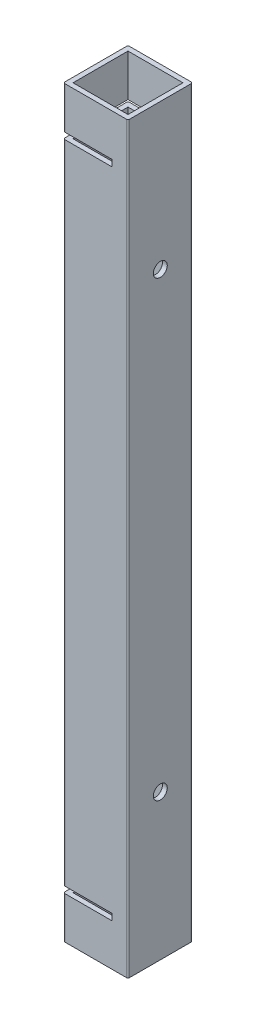
SolidWorks part; units mm, degrees
ref_plane "Front Plane" through (0, 0, 0) normal (0, 0, 1) x (1, 0, 0)
ref_plane "Top Plane" through (0, 0, 0) normal (0, 1, 0) x (1, 0, 0)
ref_plane "Right Plane" through (0, 0, 0) normal (1, 0, 0) x (0, 0, -1)
sketch "Sketch1" plane through (0, 0, 0) normal (0, 1, 0) x (1, 0, 0)
  line L0 (1.5, 1.5) -> (18.5, 1.5)
  line L1 (0.5, 0) -> (19.5, 0)
  line L2 (0, 0.5) -> (0, 19.5)
  line L3 (0.5, 20) -> (19.5, 20)
  line L4 (20, 0.5) -> (20, 19.5)
  line L5 (18.5, 1.5) -> (18.5, 18.5)
  line L6 (1.5, 18.5) -> (18.5, 18.5)
  line L7 (1.5, 1.5) -> (1.5, 18.5)
  arc A0 (19.5, 0) -> (20, 0.5) centre (19.5, 0.5) ccw
  arc A1 (0.5, 0) -> (0, 0.5) centre (0.5, 0.5) cw
  arc A2 (0, 19.5) -> (0.5, 20) centre (0.5, 19.5) cw
  arc A3 (19.5, 20) -> (20, 19.5) centre (19.5, 19.5) cw
  arc A4 (18.5, 1.5) -> (18.5, 1.5) centre (18.5, 1.5) ccw
  arc A5 (18.5, 18.5) -> (18.5, 18.5) centre (18.5, 18.5) cw
  arc A6 (1.5, 18.5) -> (1.5, 18.5) centre (1.5, 18.5) cw
  arc A7 (1.5, 1.5) -> (1.5, 1.5) centre (1.5, 1.5) cw
  point P9 (0, 0)
  dimension "D3" = 0.5
  dimension "D1" = 20
  dimension "D2" = 20
  dimension "D4" = 1.5
extrude "Boss-Extrude1" add sketch "Sketch1" along normal blind 230
sketch "Sketch2" plane through (0, 0, 0) normal (-1, 0, 0) x (0, 0, 1)
  line L0 (-0.5, 115) -> (-19.5, 115) construction
  line L5 (-0.5, 230) -> (-0.5, 0) construction
  line L6 (-19.5, 230) -> (-19.5, 0) construction
  line L12 (0, 15) -> (-20, 15)
  line L18 (0, 230) -> (0, 0) construction
  line L19 (-20, 230) -> (-20, 0) construction
  line L20 (-20, 15) -> (-20, 13)
  line L21 (-20, 13) -> (0, 13)
  line L22 (0, 13) -> (0, 15)
  line L23 (0, 217) -> (0, 215)
  line L24 (-20, 217) -> (0, 217)
  line L25 (-20, 215) -> (-20, 217)
  line L26 (0, 215) -> (-20, 215)
  dimension "D1" = 2
  dimension "D2" = 100
extrude "Cut-Extrude1" cut sketch "Sketch2" against normal blind 15
sketch "Sketch3" plane through (20, 0, 0) normal (1, 0, 0) x (0, 0, -1)
  line L0 (19.5, 115) -> (0, 115) construction
  line L1 (19.5, 230) -> (19.5, 0) construction
  line L2 (0, 230) -> (0, 0) construction
  line L3 (0.5, 230) -> (19.5, 230) construction
  circle A0 centre (10, 185) radius 2.15
  circle A1 centre (10, 45) radius 2.15
  point P8 (0, 0)
  point P11 (10, 230)
  dimension "D1" = 4.3
  dimension "D2" = 45
extrude "Cut-Extrude2" cut sketch "Sketch3" against normal through all
